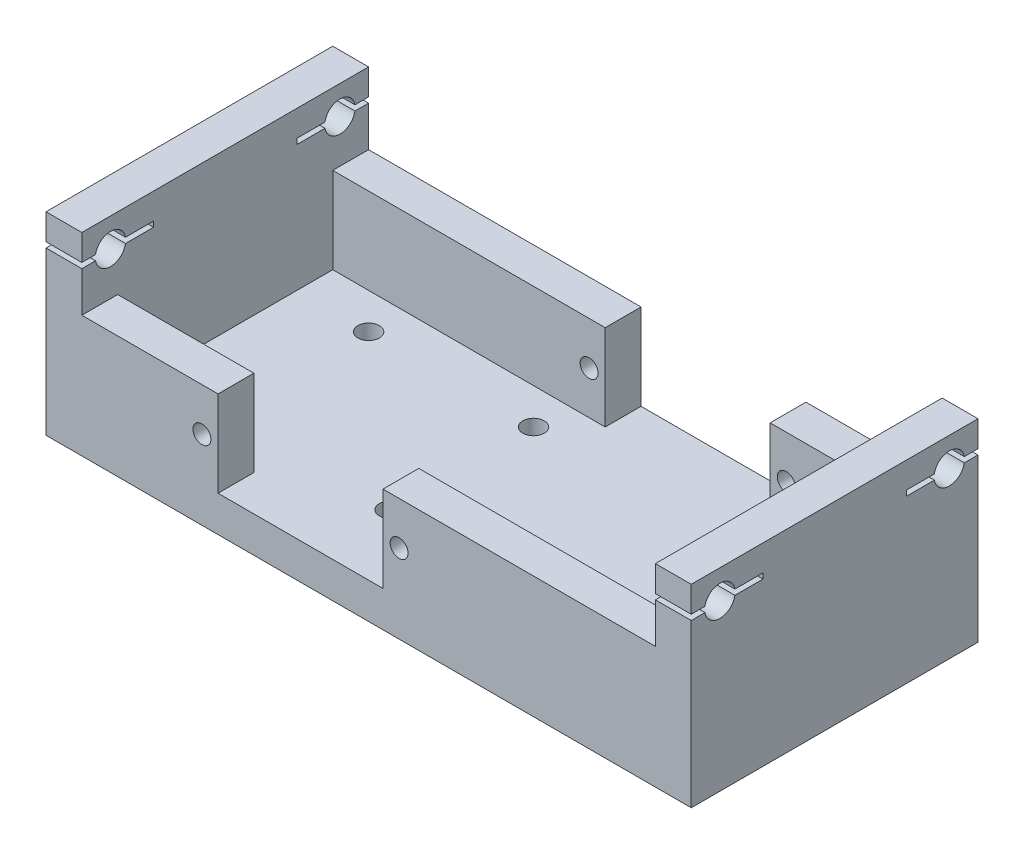
SolidWorks part; units mm, degrees
ref_plane "Front Plane" through (0, 0, 0) normal (0, 0, 1) x (1, 0, 0)
ref_plane "Top Plane" through (0, 0, 0) normal (0, 1, 0) x (1, 0, 0)
ref_plane "Right Plane" through (0, 0, 0) normal (1, 0, 0) x (0, 0, -1)
sketch "Sketch1" plane through (0, 0, 0) normal (0, 1, 0) x (1, 0, 0)
  line L1 (-45, -20) -> (45, -20)
  line L2 (-45, -20) -> (-45, 20)
  line L3 (-45, 20) -> (45, 20)
  line L4 (45, -20) -> (45, 20)
  line L5 (-45, -20) -> (45, 20) construction
  line L6 (-45, 20) -> (45, -20) construction
  point P0 (0, 0)
  dimension "D1" = 90
  dimension "D2" = 40
extrude "Boss-Extrude1" add sketch "Sketch1" along normal blind 5
sketch "Sketch2" plane through (0, 5, 0) normal (0, 1, 0) x (1, 0, 0)
  line L0 (-21, -20) -> (-21, -15)
  line L1 (-45, -20) -> (45, -20) construction
  line L2 (-21, -15) -> (-40, -15)
  line L3 (-45, 20) -> (-45, -20) construction
  line L4 (-40, -15) -> (-40, 15)
  line L6 (-40, 15) -> (-2, 15)
  line L7 (-2, 15) -> (-2, 20)
  line L8 (45, 20) -> (-45, 20) construction
  line L9 (-2, 20) -> (-45, 20)
  line L10 (-45, 20) -> (-45, -20)
  line L11 (-45, -20) -> (-21, -20)
  line L12 (2, -15) -> (40, -15)
  line L13 (45, -20) -> (45, 20) construction
  line L14 (40, -15) -> (40, 15)
  line L15 (40, 15) -> (21, 15)
  line L16 (21, 15) -> (21, 20)
  line L17 (21, 20) -> (45, 20)
  line L18 (45, 20) -> (45, -20)
  line L19 (45, -20) -> (2, -20)
  line L20 (2, -20) -> (2, -15)
  dimension "D1" = 23
  dimension "D2" = 5
  dimension "D3" = 30
  dimension "D4" = 5
  dimension "D5" = 5
  dimension "D6" = 24
  dimension "D9" = 5
extrude "Boss-Extrude2" add sketch "Sketch2" along normal blind 12
sketch "Sketch3" plane through (0, 17, 0) normal (0, 1, 0) x (1, 0, 0)
  line L0 (45, 20) -> (21, 20) construction
  line L1 (45, -20) -> (40, -20)
  line L2 (45, -20) -> (45, 20)
  line L3 (45, 20) -> (40, 20)
  line L4 (40, -20) -> (40, 20)
  line L5 (40, 15) -> (40, -15) construction
  line L6 (-45, -20) -> (-21, -20) construction
  line L7 (-45, 20) -> (-40, 20)
  line L8 (-45, 20) -> (-45, -20)
  line L9 (-45, -20) -> (-40, -20)
  line L10 (-40, 20) -> (-40, -20)
  line L11 (-40, -15) -> (-40, 15) construction
extrude "Boss-Extrude3" add sketch "Sketch3" along normal blind 10
sketch "Sketch5" plane through (-45, 0, 0) normal (-1, 0, 0) x (0, 0, 1)
  line L0 (-20, 27) -> (20, 27) construction
  line L1 (20, 27) -> (20, 0) construction
  line L2 (0, -14.85) -> (0, 14.85) construction
  circle A0 centre (16, 23) radius 2.125
  circle A1 centre (-16, 23) radius 2.125
  dimension "D1" = 4.25
  dimension "D2" = 4
  dimension "D3" = 4
extrude "Cut-Extrude1" cut sketch "Sketch5" against normal through all
sketch "Sketch7" plane through (0, 0, 15) normal (0, 0, -1) x (-1, 0, 0)
  line L0 (-21, 17) -> (-21, 5) construction
  line L1 (2, 17) -> (2, 5) construction
  line L2 (2, 17) -> (40, 17) construction
  line L3 (-40, 17) -> (-21, 17) construction
  circle A0 centre (-23.25, 11) radius 1.25
  circle A1 centre (4.25, 11) radius 1.25
  dimension "D1" = 2.5
  dimension "D2" = 2.25
  dimension "D4" = 6
  dimension "D5" = 2.5
  dimension "D6" = 6
  dimension "D3" = 2.25
extrude "Cut-Extrude3" cut sketch "Sketch7" along normal up to surface (35 mm away) up to face at (3.1667, 15.5, -20)
sketch "Sketch8" plane through (-45, 0, 0) normal (-1, 0, 0) x (0, 0, 1)
  line L0 (20, 27) -> (20, 0) construction
  line L1 (20, 23.375) -> (10, 23.375)
  line L2 (20, 23.375) -> (20, 22.625)
  line L3 (20, 22.625) -> (10, 22.625)
  line L4 (-20, 23.375) -> (-20, 22.625)
  line L5 (-20, 27) -> (-20, 0) construction
  line L6 (10, 23.375) -> (10, 22.625)
  line L7 (-10, 23.375) -> (-10, 22.625)
  line L8 (-10, 23.375) -> (-20, 23.375)
  line L9 (-10, 22.625) -> (-20, 22.625)
  circle A0 centre (16, 23) radius 2.125 construction
  dimension "D1" = 0.75
  dimension "D2" = 0.375
  dimension "D3" = 10
  dimension "D4" = 10
extrude "Cut-Extrude4" cut sketch "Sketch8" against normal through all
sketch "Sketch9" [suppressed] plane through (0, 0, 0) normal (0, -1, 0) x (-1, 0, 0)
  line L0 (45, -20) -> (-45, -20) construction
  line L1 (23.5, -20) -> (19.5, -20)
  line L2 (23.5, -20) -> (23.5, 20)
  line L3 (23.5, 20) -> (19.5, 20)
  line L4 (19.5, -20) -> (19.5, 20)
  line L5 (-45, 20) -> (45, 20) construction
  line L6 (0, -20) -> (0, 19.3326) construction
  line L7 (15, -20) -> (11, -20)
  line L8 (15, -20) -> (15, 20)
  line L9 (15, 20) -> (11, 20)
  line L10 (11, -20) -> (11, 20)
  dimension "D1" = 4
  dimension "D2" = 4
  dimension "D3" = 4.5
  dimension "D4" = 15
extrude "Boss-Extrude4" [suppressed] add sketch "Sketch9" along normal blind 20
sketch "Sketch11" [suppressed] plane through (-1.6583, 0, 0) normal (-1, 0, 0) x (0, 0, 1)
  circle A1 centre (11.5, -14.5) radius 1.25
  circle A2 centre (-16, -14.5) radius 1.25
  circle A3 centre (-16, -7) radius 1.25
  circle A4 centre (11.5, -7) radius 1.25
  dimension "D1" = 2.5
  dimension "D2" = 2.5
  dimension "D3" = 2.5
  dimension "D4" = 7.5
  dimension "D5" = 2.5
  dimension "D6" = 7.5
  dimension "D7" = 27.5
extrude "Cut-Extrude5" [suppressed] cut sketch "Sketch11" against normal through all and the other way through all
sketch "Sketch12" plane through (0, 0, 0) normal (0, -1, 0) x (1, 0, 0)
  line L0 (-45, -20) -> (-45, 20) construction
  line L2 (45, -20) -> (-45, -20) construction
  line L5 (-45, 20) -> (45, 20) construction
  circle A0 centre (-30, 10) radius 1.5
  circle A1 centre (-30, -10) radius 1.5
  circle A2 centre (-7, 10) radius 1.5
  circle A3 centre (-7, -10) radius 1.5
  dimension "D1" = 3
  dimension "D2" = 3
  dimension "D3" = 15
  dimension "D4" = 23
  dimension "D6" = 10
  dimension "D7" = 3
  dimension "D9" = 10
  dimension "D10" = 3
extrude "Cut-Extrude6" cut sketch "Sketch12" against normal through all
sketch "Sketch13" plane through (0, 0, 20) normal (0, 0, 1) x (1, 0, 0)
  line L0 (-21, 17) -> (-21, 5) construction
  circle A1 centre (-23.25, 11) radius 1.25
  circle A2 centre (4.25, 11) radius 1.25
  dimension "D1" = 2.5
  dimension "D2" = 2.5
  dimension "D3" = 27.5
  dimension "D4" = 2.25
extrude "Cut-Extrude7" cut sketch "Sketch13" against normal up to surface (5 mm away) contours A1 | A2 up to face at (21, 11, 15)
